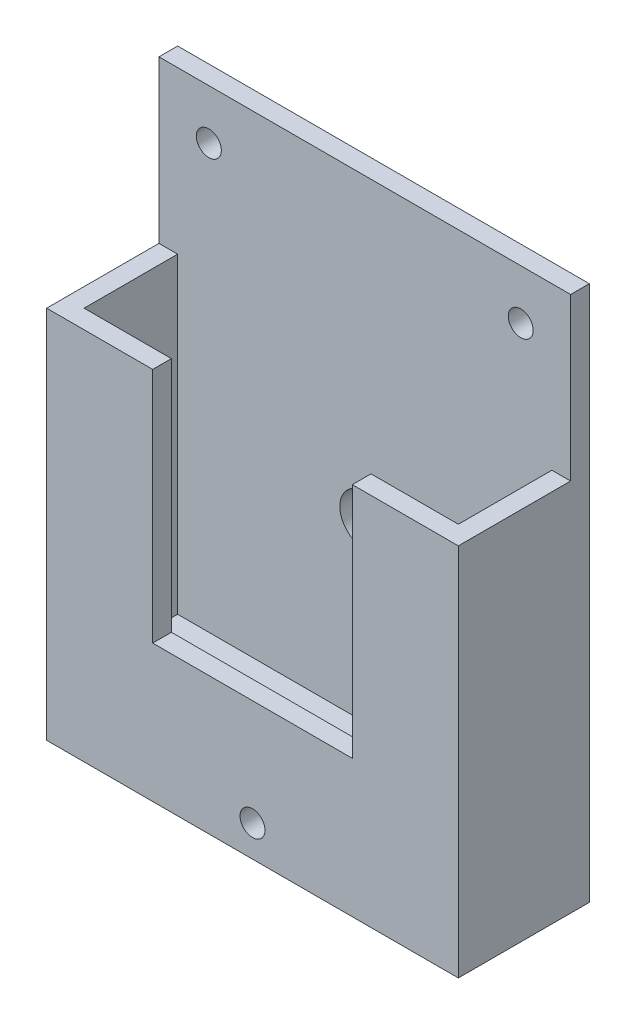
SolidWorks part; units mm, degrees
ref_plane "Front Plane" through (0, 0, 0) normal (0, 0, 1) x (1, 0, 0)
ref_plane "Top Plane" through (0, 0, 0) normal (0, 1, 0) x (1, 0, 0)
ref_plane "Right Plane" through (0, 0, 0) normal (1, 0, 0) x (0, 0, -1)
sketch "Sketch1" plane through (0, 0, 0) normal (1, 0, 0) x (0, 0, -1)
  line L16 (-3, -25.9) -> (-21, -25.9)
  line L17 (-21, -25.9) -> (-21, -85.9)
  line L20 (-21, -85.9) -> (0, -85.9)
  line L21 (0, -85.9) -> (0, 0)
  line L22 (-3, -25.9) -> (-3, 0)
  line L23 (-3, 0) -> (0, 0)
  dimension "D1" = 18
  dimension "D2" = 21
  dimension "D3" = 3
  dimension "D4" = 60
  dimension "D5" = 85.9
  dimension "D6" = 25.9
extrude "Boss-Extrude1" add sketch "Sketch1" against normal blind 66
sketch "Sketch2" plane through (0, 0, 0) normal (1, 0, 0) x (0, 0, -1)
  line L0 (-18, -25.9) -> (-18, -75.9)
  line L1 (-3, -25.9) -> (-21, -25.9) construction
  line L2 (-18, -75.9) -> (-3, -75.9)
  line L3 (-3, -75.9) -> (-3, -25.9)
  line L4 (-3, -25.9) -> (-18, -25.9)
  line L5 (-21, -85.9) -> (0, -85.9) construction
  dimension "D1" = 15
  dimension "D2" = 10
  dimension "D3" = 50
extrude "Cut-Extrude1" cut sketch "Sketch2" against normal blind 60 from offset 3 offset against normal yes
sketch "Sketch3" plane through (0, 0, 3) normal (0, 0, 1) x (1, 0, 0)
  line L0 (-49, -25.9) -> (-49, -63.9)
  line L1 (-66, -25.9) -> (0, -25.9) construction
  line L2 (-49, -63.9) -> (-17, -63.9)
  line L3 (-17, -63.9) -> (-17, -25.9)
  line L4 (-17, -25.9) -> (-49, -25.9)
  line L5 (-66, -85.9) -> (0, -85.9) construction
  dimension "D1" = 17
  dimension "D2" = 17
  dimension "D3" = 32
  dimension "D4" = 22
  dimension "D5" = 38
  dimension "D6" = 38
extrude "Cut-Extrude2" cut sketch "Sketch3" along normal through all
sketch "Sketch4" plane through (0, 0, 0) normal (0, 0, -1) x (-1, 0, 0)
  line L0 (33, 0) -> (33, -85.9) construction
  line L3 (66, 0) -> (0, 0) construction
  line L4 (66, -85.9) -> (0, -85.9) construction
  line L5 (0, -42.95) -> (66, -42.95) construction
  line L6 (0, -85.9) -> (0, 0) construction
  line L7 (66, -85.9) -> (66, 0) construction
  circle A0 centre (33, -47.9) radius 4
  circle A1 centre (33, -80.9) radius 2
  circle A2 centre (58, -8) radius 2
  circle A3 centre (8, -8) radius 2
  dimension "D6" = 8
  dimension "D7" = 4
  dimension "D8" = 4
  dimension "D9" = 4
  dimension "D1" = 8
  dimension "D2" = 8
  dimension "D3" = 8
  dimension "D4" = 8
  dimension "D5" = 38
  dimension "D10" = 5
extrude "Cut-Extrude3" cut sketch "Sketch4" against normal through all
